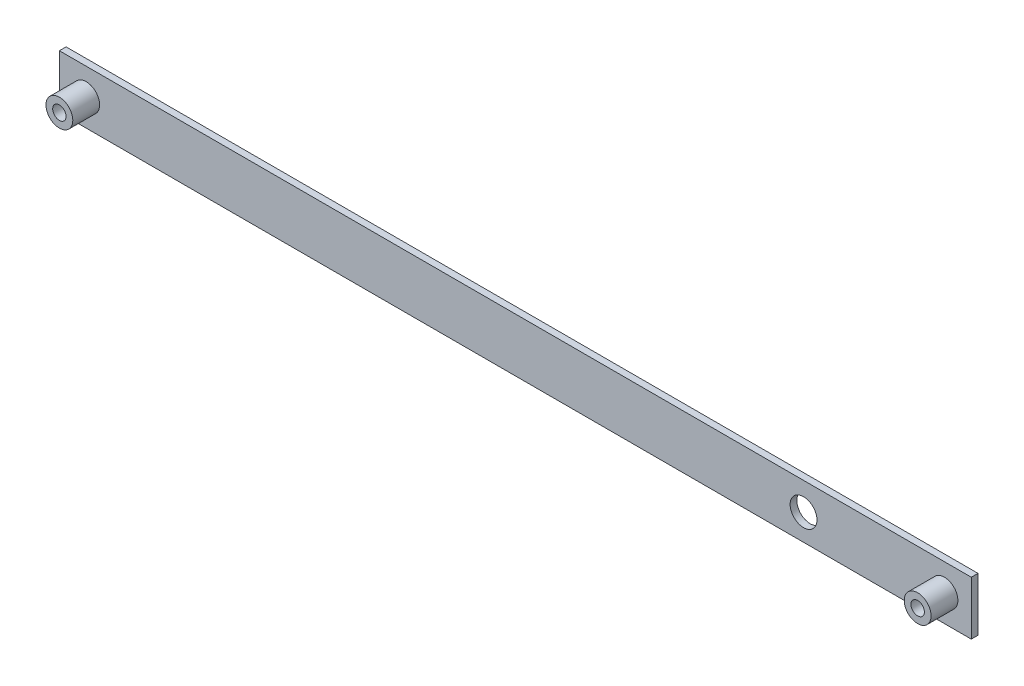
SolidWorks part; units mm, degrees
ref_plane "Front" through (0, 0, 0) normal (0, 0, 1) x (1, 0, 0)
ref_plane "Top" through (0, 0, 0) normal (0, 1, 0) x (1, 0, 0)
ref_plane "Right" through (0, 0, 0) normal (1, 0, 0) x (0, 0, -1)
sketch "Sketch1" plane through (0, 0, 0) normal (0, 0, 1) x (1, 0, 0)
  line L0 (0, 0) -> (406.4, 0) construction
  line L1 (0, 0) -> (-12.7, 0) construction
  line L2 (-12.7, 12.7) -> (419.1, 12.7)
  line L3 (-12.7, 12.7) -> (-12.7, -12.7)
  line L4 (-12.7, -12.7) -> (419.1, -12.7)
  line L5 (419.1, 12.7) -> (419.1, -12.7)
  line L6 (-12.7, 12.7) -> (419.1, -12.7) construction
  line L7 (-12.7, -12.7) -> (419.1, 12.7) construction
  line L8 (406.4, 0) -> (419.1, 0) construction
  circle A0 centre (0, 0) radius 3.175
  circle A1 centre (406.4, 0) radius 3.175
  point P5 (203.2, 0)
  dimension "D1" = 6.35
  dimension "D2" = 6.35
  dimension "D3" = 12.7
  dimension "D4" = 25.4
  dimension "D5" = 406.4
extrude "Boss-Extrude1" add sketch "Sketch1" along normal blind 3.175
sketch "Sketch2" plane through (0, 0, 3.175) normal (0, 0, 1) x (1, 0, 0)
  line L0 (406.4, 0) -> (0, 0) construction
  circle A1 centre (0, 0) radius 3.175
  circle A2 centre (0, 0) radius 6.35
  circle A3 centre (406.4, 0) radius 3.175 construction
  circle A4 centre (406.4, 0) radius 3.175
  circle A5 centre (406.4, 0) radius 6.35
  dimension "D1" = 12.7
  dimension "D2" = 12.7
  dimension "D3" = 406.4
extrude "Boss-Extrude2" add sketch "Sketch2" along normal blind 12.7
sketch "Sketch3" plane through (0, 0, 3.175) normal (0, 0, 1) x (1, 0, 0)
  circle A1 centre (339.6683, -0.34) radius 6.35
extrude "Cut-Extrude1" cut sketch "Sketch3" against normal up to next
